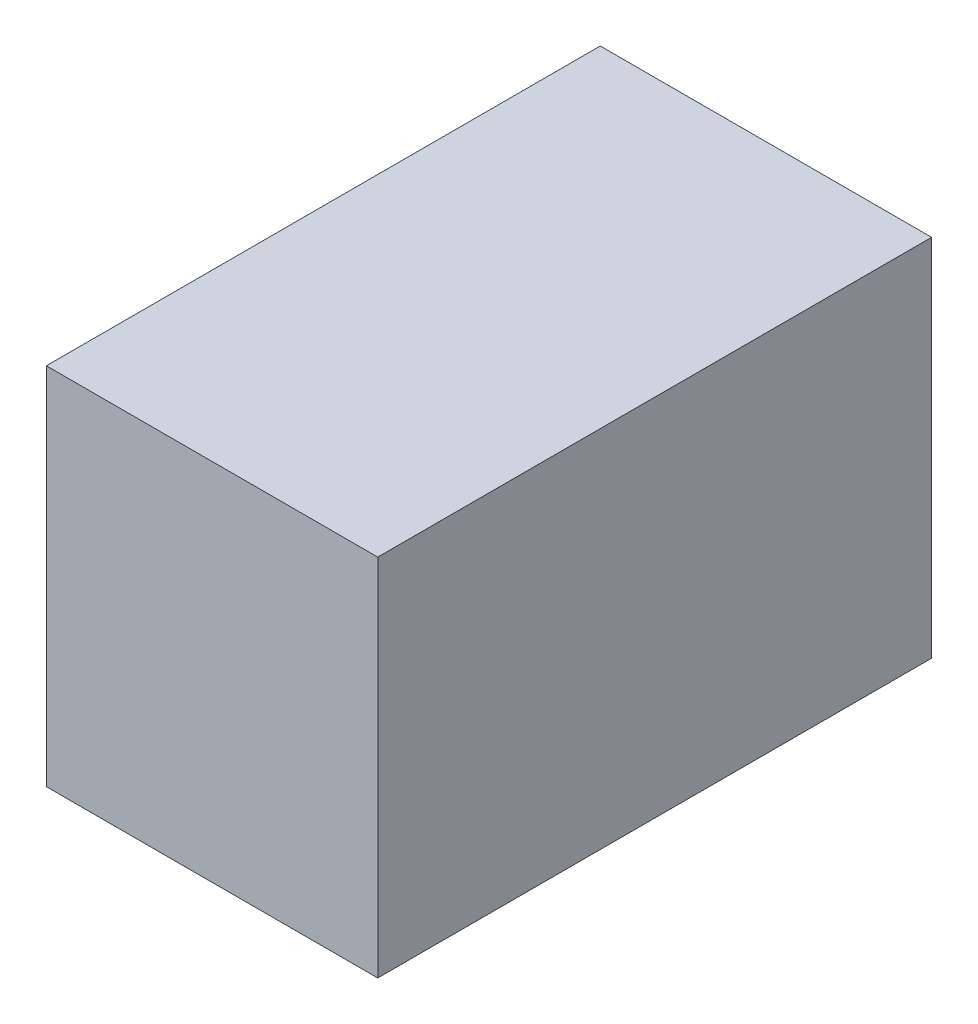
SolidWorks part; units mm, degrees
ref_plane "Front Plane" through (0, 0, 0) normal (0, 0, 1) x (1, 0, 0)
ref_plane "Top Plane" through (0, 0, 0) normal (0, 1, 0) x (1, 0, 0)
ref_plane "Right Plane" through (0, 0, 0) normal (1, 0, 0) x (0, 0, -1)
sketch "Sketch4" plane through (0, 0, 0) normal (1, 0, 0) x (0, 0, -1)
  line L1 (-15.55, 9.55) -> (15.55, 9.55)
  line L2 (-15.55, 9.55) -> (-15.55, -9.55)
  line L3 (-15.55, -9.55) -> (15.55, -9.55)
  line L4 (15.55, 9.55) -> (15.55, -9.55)
  line L5 (-15.55, 9.55) -> (15.55, -9.55) construction
  line L6 (-15.55, -9.55) -> (15.55, 9.55) construction
  point P0 (0, 0)
  dimension "D1" = 31.1
  dimension "D2" = 19.1
extrude "Boss-Extrude1" add sketch "Sketch4" along normal blind 19
shell "Shell1" thickness 2
sketch "Sketch5" plane through (0, 0, -17.55) normal (0, 0, -1) x (-1, 0, 0)
  line L0 (0, -11.55) -> (0, 11.55) construction
  line L1 (0, 9.55) -> (-12, 9.55)
  line L2 (-12, 9.55) -> (-12, -9.55)
  line L3 (-12, -9.55) -> (0, -9.55)
  line L4 (-21, 11.55) -> (0, 11.55) construction
  line L5 (-21, -11.55) -> (0, -11.55) construction
  line L6 (0, 9.55) -> (0, -9.55)
  dimension "D1" = 12
  dimension "D2" = 2
  dimension "D3" = 2
extrude "Cut-Extrude1" cut sketch "Sketch5" against normal up to surface (2 mm away) up to face at (9.5, 0, -15.55)
equation "\"terminalRad\"= 3mm"
equation "\"terminalLen\"= 10.5mm"
equation "\"threadlen\"=11"
